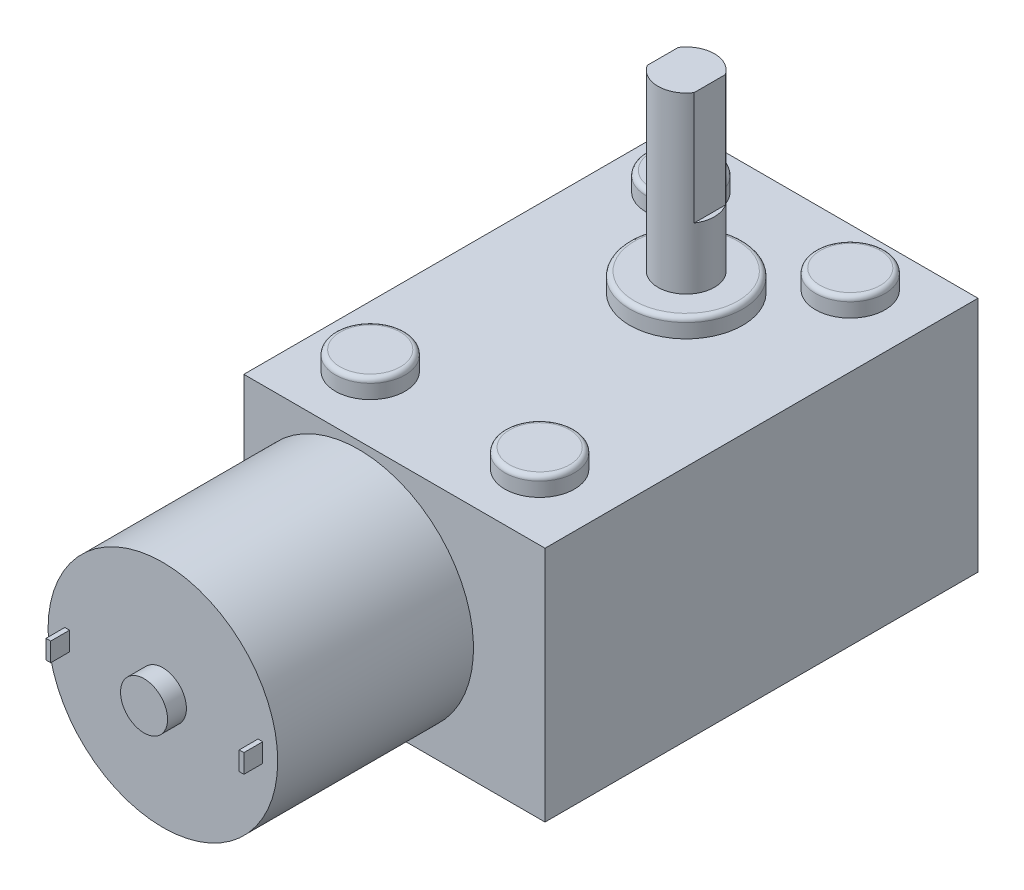
SolidWorks part; units mm, degrees
ref_plane "Alzado" through (0, 0, 0) normal (0, 0, 1) x (1, 0, 0)
ref_plane "Planta" through (0, 0, 0) normal (0, 1, 0) x (1, 0, 0)
ref_plane "Vista lateral" through (0, 0, 0) normal (1, 0, 0) x (0, 0, -1)
sketch "Croquis1" plane through (0, 0, 0) normal (0, 1, 0) x (1, 0, 0)
  line L0 (0, -25.3) -> (0, 25.3) construction
  line L1 (-16, -23) -> (16, -23)
  line L2 (-16, -23) -> (-16, 23)
  line L3 (-16, 23) -> (16, 23)
  line L4 (16, -23) -> (16, 23)
  line L5 (-16, -23) -> (16, 23) construction
  line L6 (-16, 23) -> (16, -23) construction
  circle A0 centre (-9.5691, 17) radius 3.7
  circle A1 centre (8.4309, 17) radius 3.7
  circle A2 centre (-9.5691, -16) radius 3.7
  circle A3 centre (8.4309, -16) radius 3.7
  circle A4 centre (0, 8) radius 6
  point P0 (0, 0)
  dimension "D3" = 7.4
  dimension "D9" = 12
  dimension "D1" = 46
  dimension "D2" = 32
  dimension "D4" = 6
  dimension "D5" = 18
  dimension "D6" = 7
  dimension "D7" = 7
  dimension "D8" = 9
  dimension "D10" = 33
extrude "Saliente-Extruir1" add sketch "Croquis1" along normal blind 25.2 contours L1 L4 L3 L2 A4 A3 A2 A1 A0 | A4 | A0 | A1 | A2 | A3
sketch "Croquis2" plane through (0, 25.2, 0) normal (0, 1, 0) x (1, 0, 0)
  circle A0 centre (-9.5691, 17) radius 3.7
  circle A1 centre (8.4309, 17) radius 3.7
  circle A2 centre (8.4309, -16) radius 3.7
  circle A3 centre (-9.5691, -16) radius 3.7
  circle A4 centre (0, 8) radius 6
extrude "Saliente-Extruir2" add sketch "Croquis2" along normal blind 2
sketch "Croquis3" plane through (0, 0, 23) normal (0, 0, 1) x (1, 0, 0)
  line L0 (-16, 25.2) -> (-16, 0) construction
  line L1 (17.6, 0) -> (-17.6, 0) construction
  circle A0 centre (-3.8, 12.2) radius 12.2
  dimension "D1" = 24.4
extrude "Saliente-Extruir3" add sketch "Croquis3" along normal blind 20.8
sketch "Croquis4" plane through (0, 0, 43.8) normal (0, 0, 1) x (1, 0, 0)
  circle A0 centre (-3.8, 12.2) radius 2.5
  dimension "D1" = 5
extrude "Saliente-Extruir4" add sketch "Croquis4" along normal blind 2 contours A0
sketch "Croquis5" plane through (0, 0, 43.8) normal (0, 0, 1) x (1, 0, 0)
  line L0 (-3.8, 12.2) -> (3.2785, 12.2) construction
  line L1 (6.3093, 13.2) -> (6.8093, 13.2)
  line L2 (6.3093, 13.2) -> (6.3093, 11.2)
  line L3 (6.3093, 11.2) -> (6.8093, 11.2)
  line L4 (6.8093, 13.2) -> (6.8093, 11.2)
  line L5 (6.3093, 13.2) -> (6.8093, 11.2) construction
  line L6 (6.3093, 11.2) -> (6.8093, 13.2) construction
  line L7 (-13.718, 13.2) -> (-14.218, 13.2)
  line L8 (-13.718, 13.2) -> (-13.718, 11.2)
  line L9 (-13.718, 11.2) -> (-14.218, 11.2)
  line L10 (-14.218, 13.2) -> (-14.218, 11.2)
  line L11 (-13.718, 13.2) -> (-14.218, 11.2) construction
  line L12 (-13.718, 11.2) -> (-14.218, 13.2) construction
  point P0 (6.5593, 12.2)
  point P5 (-13.968, 12.2)
  dimension "D1" = 2
  dimension "D2" = 0.5
extrude "Saliente-Extruir5" add sketch "Croquis5" along normal blind 2
sketch "Croquis6" plane through (0, 27.2, 0) normal (0, 1, 0) x (1, 0, 0)
  circle A0 centre (0, 8) radius 3
  dimension "D1" = 6
extrude "Saliente-Extruir6" add sketch "Croquis6" along normal blind 18.5
sketch "Croquis7" plane through (0, 45.7, 0) normal (0, 1, 0) x (1, 0, 0)
  line L2 (-2.5, 6.3417) -> (-2.5, 9.6583)
  line L4 (2.5, 6.3417) -> (2.5, 9.6583)
  arc A0 (-2.5, 9.6583) -> (-2.5, 6.3417) centre (0, 8) ccw
  arc A1 (2.5, 6.3417) -> (2.5, 9.6583) centre (0, 8) ccw
extrude "Cortar-Extruir1" cut sketch "Croquis7" against normal blind 12
fillet "Redondeo2" radius 0.5 5 edges at (-9.5691, 27.2, -13.3) (8.4309, 27.2, -13.3) (0, 27.2, -2) (-9.5691, 27.2, 19.7) (8.4309, 27.2, 19.7)
